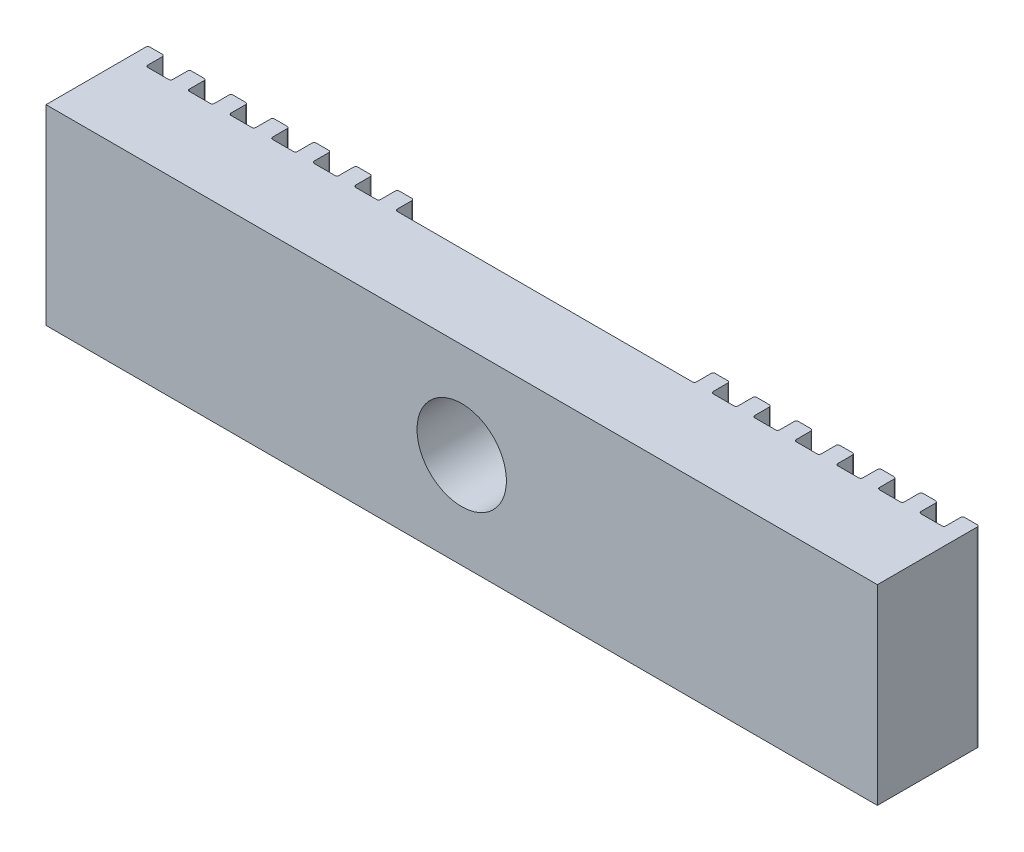
SolidWorks part; units mm, degrees
other "Câmera1"
ref_plane "Plano frontal" through (0, 0, 0) normal (0, 0, 1) x (1, 0, 0)
ref_plane "Plano superior" through (0, 0, 0) normal (0, 1, 0) x (1, 0, 0)
ref_plane "Plano direito" through (0, 0, 0) normal (1, 0, 0) x (0, 0, -1)
sketch "Esboço4" plane through (0, 0, 0) normal (0, 1, 0) x (1, 0, 0)
  line L0 (-19.2, 2.35) -> (-19.2, 1.65)
  line L1 (-20, -2.45) -> (20, -2.45)
  line L2 (-20, -2.45) -> (-20, 2.35)
  line L3 (-19.9, 2.45) -> (-19.3, 2.45)
  line L4 (20, -2.45) -> (20, 2.35)
  line L5 (-19.1, 1.55) -> (-18.1, 1.55)
  line L6 (19.2, 2.35) -> (19.2, 1.65)
  line L7 (19.3, 2.45) -> (19.9, 2.45)
  line L8 (-18, 1.65) -> (-18, 2.35)
  line L9 (-17.9, 2.45) -> (-17.3, 2.45)
  line L10 (-17.2, 2.35) -> (-17.2, 1.65)
  line L11 (-16, 1.65) -> (-16, 2.35)
  line L12 (-15.9, 2.45) -> (-15.3, 2.45)
  line L13 (-15.2, 2.35) -> (-15.2, 1.65)
  line L14 (-14, 1.65) -> (-14, 2.35)
  line L15 (-13.9, 2.45) -> (-13.3, 2.45)
  line L16 (-13.2, 2.35) -> (-13.2, 1.65)
  line L17 (-12, 1.65) -> (-12, 2.35)
  line L18 (-11.9, 2.45) -> (-11.3, 2.45)
  line L19 (-11.2, 2.35) -> (-11.2, 1.65)
  line L20 (-10, 1.65) -> (-10, 2.35)
  line L21 (-9.9, 2.45) -> (-9.3, 2.45)
  line L22 (-9.2, 2.35) -> (-9.2, 1.65)
  line L23 (-8, 1.65) -> (-8, 2.35)
  line L24 (-7.9, 2.45) -> (-7.3, 2.45)
  line L25 (-7.2, 2.35) -> (-7.2, 1.65)
  line L26 (-7.1, 1.55) -> (7.1, 1.55)
  line L27 (-9.1, 1.55) -> (-8.1, 1.55)
  line L28 (-11.1, 1.55) -> (-10.1, 1.55)
  line L29 (-13.1, 1.55) -> (-12.1, 1.55)
  line L30 (-15.1, 1.55) -> (-14.1, 1.55)
  line L31 (-17.1, 1.55) -> (-16.1, 1.55)
  line L32 (17.2, 2.35) -> (17.2, 1.65)
  line L33 (17.3, 2.45) -> (17.9, 2.45)
  line L34 (18, 1.65) -> (18, 2.35)
  line L35 (15.2, 2.35) -> (15.2, 1.65)
  line L36 (15.3, 2.45) -> (15.9, 2.45)
  line L37 (16, 1.65) -> (16, 2.35)
  line L38 (13.2, 2.35) -> (13.2, 1.65)
  line L39 (13.3, 2.45) -> (13.9, 2.45)
  line L40 (14, 1.65) -> (14, 2.35)
  line L41 (11.2, 2.35) -> (11.2, 1.65)
  line L42 (11.3, 2.45) -> (11.9, 2.45)
  line L43 (12, 1.65) -> (12, 2.35)
  line L44 (9.2, 2.35) -> (9.2, 1.65)
  line L45 (9.3, 2.45) -> (9.9, 2.45)
  line L46 (10, 1.65) -> (10, 2.35)
  line L47 (7.2, 2.35) -> (7.2, 1.65)
  line L48 (7.3, 2.45) -> (7.9, 2.45)
  line L49 (8, 1.65) -> (8, 2.35)
  line L50 (8.1, 1.55) -> (9.1, 1.55)
  line L51 (10.1, 1.55) -> (11.1, 1.55)
  line L52 (12.1, 1.55) -> (13.1, 1.55)
  line L53 (14.1, 1.55) -> (15.1, 1.55)
  line L54 (16.1, 1.55) -> (17.1, 1.55)
  line L55 (18.1, 1.55) -> (19.1, 1.55)
  arc A0 (19.9, 2.45) -> (20, 2.35) centre (19.9, 2.35) cw
  arc A1 (19.2, 2.35) -> (19.3, 2.45) centre (19.3, 2.35) cw
  arc A2 (19.1, 1.55) -> (19.2, 1.65) centre (19.1, 1.65) ccw
  arc A3 (18.1, 1.55) -> (18, 1.65) centre (18.1, 1.65) cw
  arc A4 (17.9, 2.45) -> (18, 2.35) centre (17.9, 2.35) cw
  arc A5 (17.2, 2.35) -> (17.3, 2.45) centre (17.3, 2.35) cw
  arc A6 (17.2, 1.65) -> (17.1, 1.55) centre (17.1, 1.65) cw
  arc A7 (16.1, 1.55) -> (16, 1.65) centre (16.1, 1.65) cw
  arc A8 (15.9, 2.45) -> (16, 2.35) centre (15.9, 2.35) cw
  arc A9 (15.2, 2.35) -> (15.3, 2.45) centre (15.3, 2.35) cw
  arc A10 (15.2, 1.65) -> (15.1, 1.55) centre (15.1, 1.65) cw
  arc A11 (14, 1.65) -> (14.1, 1.55) centre (14.1, 1.65) ccw
  arc A12 (13.9, 2.45) -> (14, 2.35) centre (13.9, 2.35) cw
  arc A13 (13.2, 2.35) -> (13.3, 2.45) centre (13.3, 2.35) cw
  arc A14 (13.2, 1.65) -> (13.1, 1.55) centre (13.1, 1.65) cw
  arc A15 (12, 1.65) -> (12.1, 1.55) centre (12.1, 1.65) ccw
  arc A16 (11.9, 2.45) -> (12, 2.35) centre (11.9, 2.35) cw
  arc A17 (11.2, 2.35) -> (11.3, 2.45) centre (11.3, 2.35) cw
  arc A18 (11.2, 1.65) -> (11.1, 1.55) centre (11.1, 1.65) cw
  arc A19 (10, 1.65) -> (10.1, 1.55) centre (10.1, 1.65) ccw
  arc A20 (9.9, 2.45) -> (10, 2.35) centre (9.9, 2.35) cw
  arc A21 (9.2, 2.35) -> (9.3, 2.45) centre (9.3, 2.35) cw
  arc A22 (9.2, 1.65) -> (9.1, 1.55) centre (9.1, 1.65) cw
  arc A23 (8, 1.65) -> (8.1, 1.55) centre (8.1, 1.65) ccw
  arc A24 (7.9, 2.45) -> (8, 2.35) centre (7.9, 2.35) cw
  arc A25 (7.2, 2.35) -> (7.3, 2.45) centre (7.3, 2.35) cw
  arc A26 (7.2, 1.65) -> (7.1, 1.55) centre (7.1, 1.65) cw
  arc A27 (-7.2, 1.65) -> (-7.1, 1.55) centre (-7.1, 1.65) ccw
  arc A28 (-7.3, 2.45) -> (-7.2, 2.35) centre (-7.3, 2.35) cw
  arc A29 (-8, 1.65) -> (-8.1, 1.55) centre (-8.1, 1.65) cw
  arc A30 (-8, 2.35) -> (-7.9, 2.45) centre (-7.9, 2.35) cw
  arc A31 (-9.2, 1.65) -> (-9.1, 1.55) centre (-9.1, 1.65) ccw
  arc A32 (-9.3, 2.45) -> (-9.2, 2.35) centre (-9.3, 2.35) cw
  arc A33 (-10, 2.35) -> (-9.9, 2.45) centre (-9.9, 2.35) cw
  arc A34 (-10, 1.65) -> (-10.1, 1.55) centre (-10.1, 1.65) cw
  arc A35 (-11.2, 1.65) -> (-11.1, 1.55) centre (-11.1, 1.65) ccw
  arc A36 (-11.3, 2.45) -> (-11.2, 2.35) centre (-11.3, 2.35) cw
  arc A37 (-12, 1.65) -> (-12.1, 1.55) centre (-12.1, 1.65) cw
  arc A38 (-12, 2.35) -> (-11.9, 2.45) centre (-11.9, 2.35) cw
  arc A39 (-13.2, 1.65) -> (-13.1, 1.55) centre (-13.1, 1.65) ccw
  arc A40 (-13.3, 2.45) -> (-13.2, 2.35) centre (-13.3, 2.35) cw
  arc A41 (-14, 1.65) -> (-14.1, 1.55) centre (-14.1, 1.65) cw
  arc A42 (-14, 2.35) -> (-13.9, 2.45) centre (-13.9, 2.35) cw
  arc A43 (-15.2, 1.65) -> (-15.1, 1.55) centre (-15.1, 1.65) ccw
  arc A44 (-15.3, 2.45) -> (-15.2, 2.35) centre (-15.3, 2.35) cw
  arc A45 (-16, 1.65) -> (-16.1, 1.55) centre (-16.1, 1.65) cw
  arc A46 (-16, 2.35) -> (-15.9, 2.45) centre (-15.9, 2.35) cw
  arc A47 (-17.2, 1.65) -> (-17.1, 1.55) centre (-17.1, 1.65) ccw
  arc A48 (-17.3, 2.45) -> (-17.2, 2.35) centre (-17.3, 2.35) cw
  arc A49 (-18, 1.65) -> (-18.1, 1.55) centre (-18.1, 1.65) cw
  arc A50 (-18, 2.35) -> (-17.9, 2.45) centre (-17.9, 2.35) cw
  arc A51 (-19.2, 1.65) -> (-19.1, 1.55) centre (-19.1, 1.65) ccw
  arc A52 (-19.2, 2.35) -> (-19.3, 2.45) centre (-19.3, 2.35) ccw
  arc A53 (-20, 2.35) -> (-19.9, 2.45) centre (-19.9, 2.35) cw
  point P0 (0, 0)
  point P62 (19.2, 2.45)
  point P83 (14, 1.55)
  point P92 (12, 1.55)
  point P101 (10, 1.55)
  point P110 (8, 1.55)
  dimension "D2" = 0.1
  dimension "D1" = 7
  dimension "D3" = 14.2
extrude "Ressalto-extrusão2" add sketch "Esboço4" along normal blind 9.2
sketch "Esboço5" plane through (0, 0, -1.55) normal (0, 0, -1) x (-1, 0, 0)
  circle A0 centre (0, 4.6) radius 2.15
  dimension "D1" = 4.3
extrude "Corte-extrusão2" cut sketch "Esboço5" against normal blind 9.2
chamfer "Chanfro2" distance 0.3 angle 45 1 edges at (-2.15, 4.6, -1.55)
